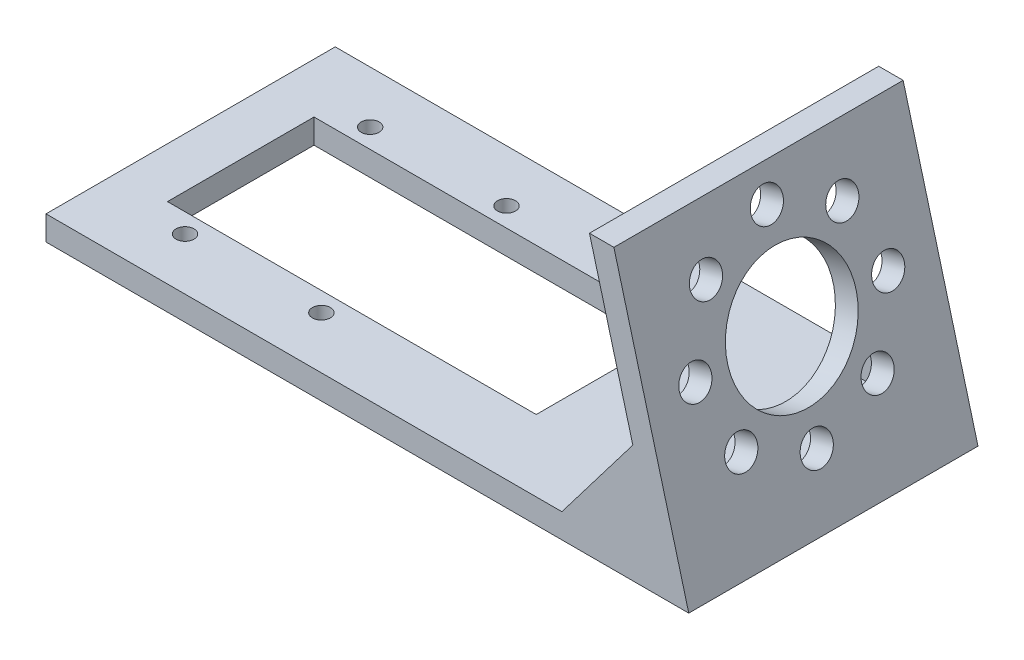
SolidWorks part; units mm, degrees
ref_plane "Front Plane" through (0, 0, 0) normal (0, 0, 1) x (1, 0, 0)
ref_plane "Top Plane" through (0, 0, 0) normal (0, 1, 0) x (1, 0, 0)
ref_plane "Right Plane" through (0, 0, 0) normal (1, 0, 0) x (0, 0, -1)
sketch "Sketch3" plane through (0, 0, 0) normal (0, 0, 1) x (1, 0, 0)
  line L0 (-49.78, 0) -> (77.22, 0)
  line L1 (77.22, 0) -> (62.4285, 55.2027)
  line L2 (62.4285, 55.2027) -> (57.6025, 55.2027)
  line L3 (57.6025, 55.2027) -> (71.1009, 4.826)
  line L4 (71.1009, 4.826) -> (-49.78, 4.826)
  line L5 (-49.78, 4.826) -> (-49.78, 0)
  point P7 (13.72, 0)
  dimension "D1" = 4.826
  dimension "D2" = 4.826
  dimension "D3" = 127
  dimension "D4" = 57.15
  dimension "D5" = 75
extrude "Boss-Extrude1" add sketch "Sketch3" along normal blind 57.15
sketch "Sketch5" plane through (0, 0, 57.15) normal (0, 0, 1) x (1, 0, 0)
  line L0 (71.1009, 4.826) -> (52.1483, 4.826)
  line L1 (71.1009, 4.826) -> (-49.78, 4.826) construction
  line L2 (52.1483, 4.826) -> (66.1704, 23.2269)
  line L3 (57.6025, 55.2027) -> (71.1009, 4.826) construction
  line L10 (-49.78, 4.826) -> (-49.78, 0)
  line L11 (-49.78, 0) -> (77.22, 0)
  line L12 (77.22, 0) -> (62.4285, 55.2027)
  line L13 (62.4285, 55.2027) -> (57.6025, 55.2027)
  line L14 (57.6025, 55.2027) -> (71.1009, 4.826)
  line L15 (71.1009, 4.826) -> (-49.78, 4.826)
  line L16 (-49.78, 4.826) -> (-49.78, 0)
  line L17 (-49.78, 0) -> (77.22, 0)
  line L18 (77.22, 0) -> (62.4285, 55.2027)
  line L19 (62.4285, 55.2027) -> (57.6025, 55.2027)
  line L20 (57.6025, 55.2027) -> (66.1704, 23.2269)
  line L21 (71.1009, 4.826) -> (-49.78, 4.826)
  line M5 (57.6025, 55.2027) -> (71.1009, 4.826)
  line M6 (71.1009, 4.826) -> (-49.78, 4.826)
  dimension "D1" = 19.05
  dimension "D2" = 18.9526
  dimension "D3" = 0
extrude "Boss-Extrude2" add sketch "Sketch5" against normal blind 4.826 contours L2 M6 M5
sketch "Sketch6" plane through (67.5445, 18.0985, 0) normal (-0.9659, -0.2588, 0) x (0, 0, 1)
  line L0 (28.575, 38.4131) -> (28.575, -13.7407) construction
  line L1 (57.15, 38.4131) -> (0, 38.4131) construction
  line L2 (52.324, -13.7407) -> (0, -13.7407) construction
  point P6 (28.575, 12.3362)
ref_plane "Plane1" through (0, 0, 28.575) normal (0, 0, -1) x (0.2588, -0.9659, 0)
mirror "Mirror1" about plane through (0, 0, 28.575) normal (0, 0, -1) of "Boss-Extrude2"
ref_plane "Plane2" through (72.0472, 19.305, 0) normal (0.9659, 0.2588, 0) x (0, 0, -1)
sketch "Sketch9" plane through (72.0472, 19.305, 0) normal (0.9659, 0.2588, 0) x (0, 0, -1)
  line L0 (-28.575, 38.4131) -> (-28.575, -13.7407) construction
  line L1 (-57.15, 37.164) -> (0, 37.164) construction
  circle A0 centre (-28.575, 11.764) radius 12.7
  dimension "D1" = 25.4
  dimension "D2" = 25.4
extrude "Cut-Extrude1" cut sketch "Sketch9" against normal up to next
sketch "Sketch11" plane through (72.0472, 19.305, 0) normal (0.9659, 0.2588, 0) x (0, 0, -1)
  circle A0 centre (-28.575, 30.814) radius 3.175
  dimension "D1" = 6.35
  dimension "D2" = 19.05
extrude "Cut-Extrude2" cut sketch "Sketch11" against normal up to next (4.6616 mm away)
pattern_circular "CirPattern1" count 8 over 360 about axis through (-3.0447, 11.3631, 28.575) along (0.9659, 0.2588, 0) of "Cut-Extrude2"
ref_plane "Plane3" through (0, 4.826, 0) normal (0, 1, 0) x (1, 0, 0)
sketch "Sketch12" plane through (0, 4.826, 0) normal (0, 1, 0) x (1, 0, 0)
  line L0 (-39.874, -6.985) -> (31.246, -6.985) construction
  line L1 (32.9884, -14.097) -> (32.9884, -43.053)
  line L2 (31.246, -50.165) -> (-39.874, -50.165) construction
  line L3 (-39.874, -43.053) -> (-39.874, -14.097)
  line L5 (-49.78, -57.15) -> (-49.78, 0) construction
  line L6 (-39.874, -14.097) -> (32.9884, -14.097)
  line L7 (-39.874, -43.053) -> (32.9884, -43.053)
  line L12 (52.1483, 0) -> (-49.78, 0) construction
  circle A0 centre (-32.5959, -46.863) radius 1.778
  circle A1 centre (-5.6551, -46.863) radius 1.778
  dimension "D8" = 3.556
  dimension "D11" = 26.9408
  dimension "D1" = 43.18
  dimension "D2" = 71.12
  dimension "D3" = 6.985
  dimension "D4" = 9.906
  dimension "D5" = 7.112
  dimension "D6" = 7.112
  dimension "D7" = 72.8624
  dimension "D9" = 7.2781
  dimension "D10" = 3.81
  dimension "D12" = 3.81
extrude "Cut-Extrude4" cut sketch "Sketch12" against normal through all
mirror "Mirror4" about plane through (0, 0, 28.575) normal (0, 0, -1) of "Cut-Extrude4"
ref_plane "Plane4" through (71.5711, 19.1774, 6.0438) normal (0.9627, 0.258, 0.0813) x (0.0841, 0, -0.9965)
